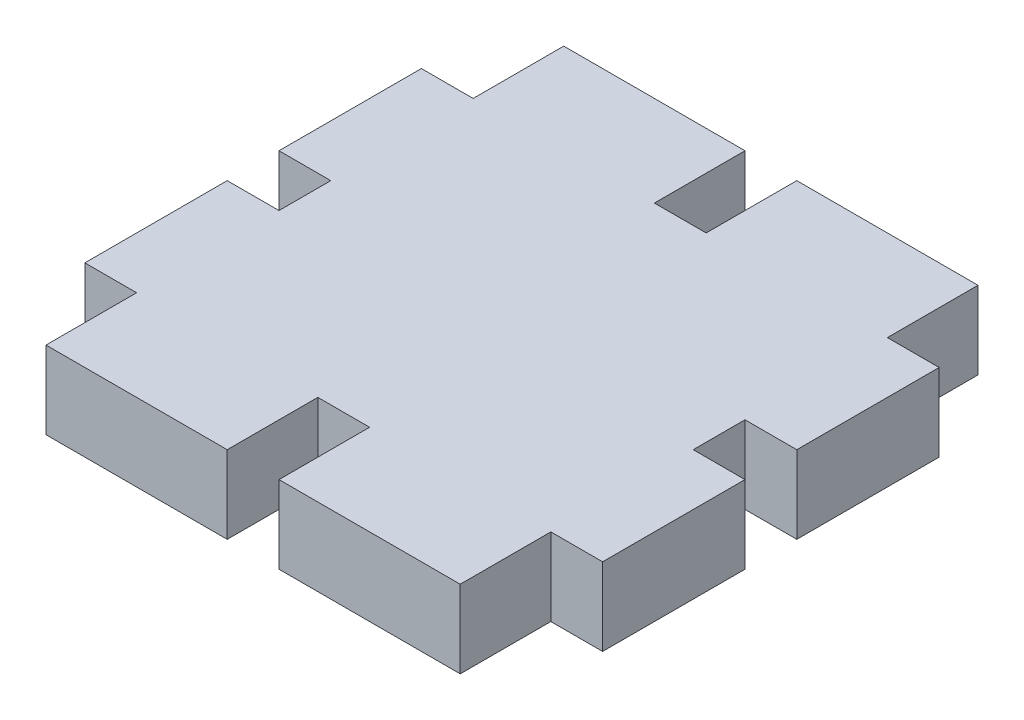
SolidWorks part; units mm, degrees
ref_plane "Alzado" through (0, 0, 0) normal (0, 0, 1) x (1, 0, 0)
ref_plane "Planta" through (0, 0, 0) normal (0, 1, 0) x (1, 0, 0)
ref_plane "Vista lateral" through (0, 0, 0) normal (1, 0, 0) x (0, 0, -1)
sketch "Sketch1" plane through (0, 0, 0) normal (0, 1, 0) x (1, 0, 0)
  line L0 (0, 22.3067) -> (0, -9.1607) construction
  line L1 (-12.3571, 0) -> (15.0357, 0) construction
  line L2 (1, 16.5) -> (-1, 16.5)
  line L3 (-1, 16.5) -> (-1, 20)
  line L4 (-1, 20) -> (-8, 20)
  line L5 (-8, 20) -> (-8, 16.5)
  line L6 (-8, 16.5) -> (-10, 16.5)
  line L7 (-10, 16.5) -> (-10, 11)
  line L8 (-10, 11) -> (-8, 11)
  line L9 (-8, 11) -> (-8, 9)
  line L10 (-8, 9) -> (-10, 9)
  line L11 (-10, 9) -> (-10, 3.5)
  line L12 (-10, 3.5) -> (-8, 3.5)
  line L13 (-8, 3.5) -> (-8, 0)
  line L14 (-8, 0) -> (-1, 0)
  line L15 (-1, 0) -> (-1, 3.5)
  line L16 (-1, 3.5) -> (1, 3.5)
  line L26 (1, 0) -> (1, 3.5)
  line L29 (8, 0) -> (1, 0)
  line L30 (8, 3.5) -> (8, 0)
  line L31 (10, 3.5) -> (8, 3.5)
  line L32 (10, 9) -> (10, 3.5)
  line L35 (8, 9) -> (10, 9)
  line L36 (8, 11) -> (8, 9)
  line L37 (10, 11) -> (8, 11)
  line L38 (10, 16.5) -> (10, 11)
  line L40 (8, 16.5) -> (10, 16.5)
  line L42 (8, 20) -> (8, 16.5)
  line L43 (1, 20) -> (8, 20)
  line L44 (1, 16.5) -> (1, 20)
  point P30 (0, 3.5)
  point P51 (0, 16.5)
extrude "Boss-Extrude1" add sketch "Sketch1" along normal blind 3 contours L44 L2 L3 L4 L5 L6 L7 L8 L9 L10 L11 L12 L13 L14 L15 L16 L26 L29 L30 L31 L32 L35 L36 L37 L38 L40 L42 L43
equation "\"Kerf\"= 0.2mm"
equation "\"width of square piece\"= 10mm"
equation "\"height of the square piece\"= 20mm"
equation "\"width of the opening\"= 2mm"
equation "\"chamfer\"= 1mm"
equation "\"tooth width\"= 5.5mm"
equation "\"mid-width of opening\"= 1mm"
equation "\"D1@Sketch1\"=\"mid-width of opening\""
equation "\"D2@Sketch1\"=\"width of square piece\""
equation "\"D3@Sketch1\"=\"height of the square piece\""
equation "\"D4@Sketch1\"=\"tooth width\""
equation "\"D5@Sketch1\"=\"width of the opening\""
equation "\"D6@Sketch1\"=\"width of the opening\""
